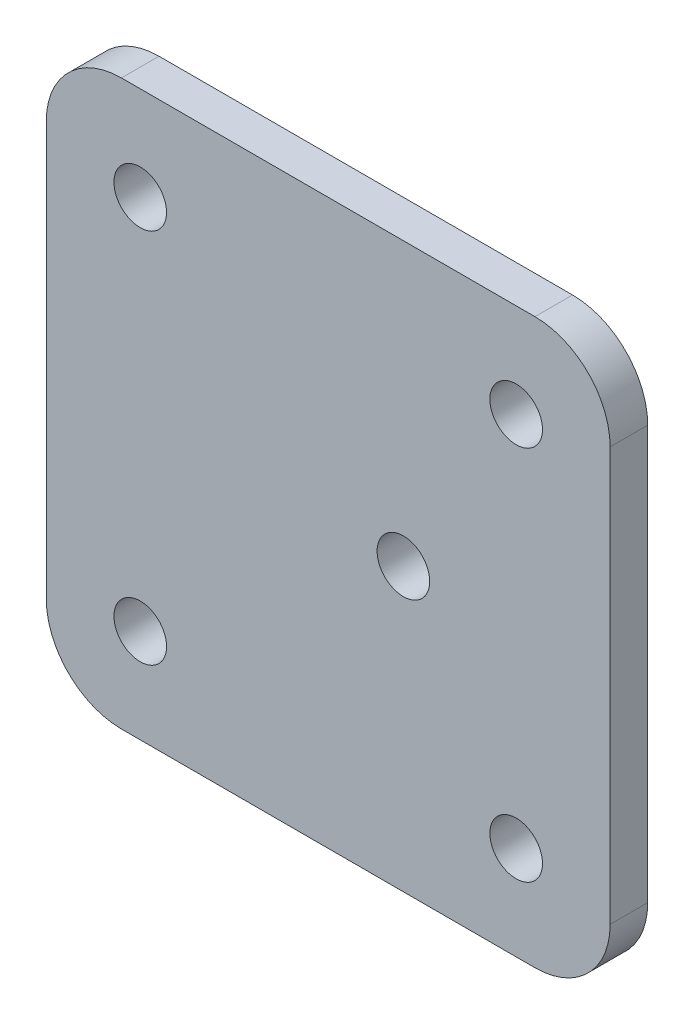
SolidWorks part; units mm, degrees
ref_plane "Front Plane" through (0, 0, 0) normal (0, 0, 1) x (1, 0, 0)
ref_plane "Top Plane" through (0, 0, 0) normal (0, 1, 0) x (1, 0, 0)
ref_plane "Right Plane" through (0, 0, 0) normal (1, 0, 0) x (0, 0, -1)
sketch "Sketch1" plane through (0, 0, 0) normal (0, 0, 1) x (1, 0, 0)
  line L0 (-36.5658, 0) -> (63.1228, 0) construction
  line L1 (0, 43.3719) -> (0, -42.4377) construction
  line L2 (-37.5, 37.5) -> (37.5, 37.5)
  line L3 (-37.5, 37.5) -> (-37.5, -37.5)
  line L4 (-37.5, -37.5) -> (37.5, -37.5)
  line L5 (37.5, 37.5) -> (37.5, -37.5)
  dimension "D1" = 75
extrude "Boss-Extrude1" add sketch "Sketch1" along normal blind 5
sketch "Sketch2" plane through (0, 0, 5) normal (0, 0, 1) x (1, 0, 0)
  line L0 (0, 39.5963) -> (0, -41.4866) construction
  line L1 (-42.2825, 0) -> (50.8385, 0) construction
  point P5 (-25, 25)
  point P6 (25, 25)
  point P7 (25, -25)
  point P8 (-25, -25)
  dimension "D1" = 50
  dimension "D2" = 50
hole_wizard "Ø7.0 (7) Diameter Hole2" positions "Sketch3" profile "Sketch4" hole size "Ø7.0" standard "ISO" end condition through all
sketch "Sketch3" plane through (0, 0, 5) normal (0, 0, 1) x (1, 0, 0)
  point P0 (-25, 25)
  point P3 (-25, -25)
  point P6 (25, -25)
  point P9 (25, 25)
sketch "Sketch4" plane through (-25, 25, 5) normal (1, 0, 0) x (0, -1, 0)
  line L0 (0, 0) -> (0, 5)
  line L1 (0, 5) -> (3.5, 5)
  line L2 (3.5, 5) -> (3.5, 0)
  line L5 (3.5, 0) -> (0, 0)
  line L11 (0, -6.35) -> (0, 107.95) construction
  dimension "Thru Hole Dia." = 7
  dimension "Thru Hole Depth" = 5
fillet "Fillet1" radius 10 4 edges at (-37.5, 37.5, 2.5) (-37.5, -37.5, 2.5) (37.5, -37.5, 2.5) (37.5, 37.5, 2.5)
sketch "Sketch5" plane through (0, 0, 5) normal (0, 0, 1) x (1, 0, 0)
  circle A0 centre (25, 25) radius 3.5 construction
  point P0 (10, 0)
  dimension "D1" = 15
hole_wizard "Ø7.0 (7) Diameter Hole1" positions "Sketch8" profile "Sketch7" hole size "Ø7.0" standard "ISO" end condition through all
sketch "Sketch8" plane through (0, 0, 5) normal (0, 0, 1) x (1, 0, 0)
  point P0 (10, 0)
sketch "Sketch7" plane through (10, 0, 5) normal (1, 0, 0) x (0, -1, 0)
  line L0 (0, 0) -> (0, 5)
  line L1 (0, 5) -> (3.5, 5)
  line L2 (3.5, 5) -> (3.5, 0)
  line L5 (3.5, 0) -> (0, 0)
  line L11 (0, -6.35) -> (0, 107.95) construction
  dimension "Thru Hole Dia." = 7
  dimension "Thru Hole Depth" = 5
